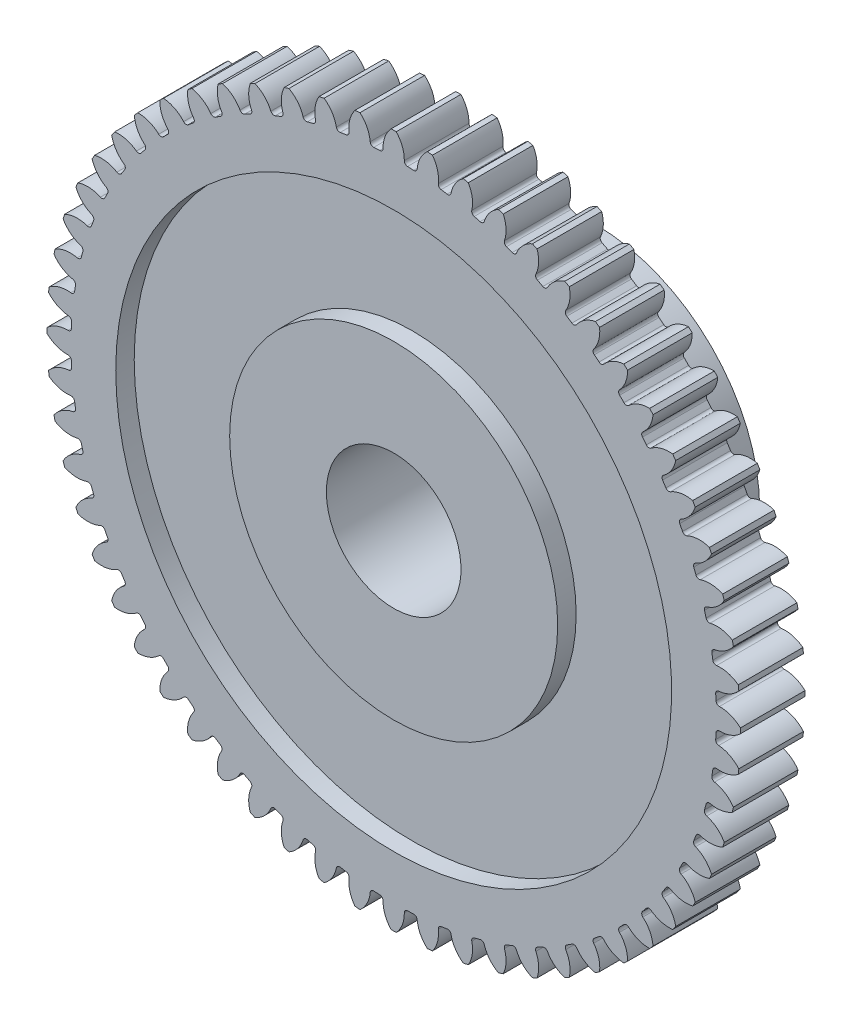
SolidWorks part; units mm, degrees
ref_plane "Front Plane" through (0, 0, 0) normal (0, 0, 1) x (1, 0, 0)
ref_plane "Top Plane" through (0, 0, 0) normal (0, 1, 0) x (1, 0, 0)
ref_plane "Right Plane" through (0, 0, 0) normal (1, 0, 0) x (0, 0, -1)
sketch "Sketch1" plane through (0, 0, 0) normal (1, 0, 0) x (0, 0, -1)
  line L0 (-4.7625, 0) -> (-4.7625, 16.3512)
  line L1 (-4.7625, 16.3512) -> (-1.7145, 16.3512)
  line L2 (-1.7145, 16.3512) -> (-1.7145, 7.7343)
  line L3 (-1.7145, 7.7343) -> (4.7625, 7.7343)
  line L4 (4.7625, 7.7343) -> (4.7625, 0)
  line L5 (4.7625, 0) -> (-4.7625, 0) construction
  line L6 (-4.7625, 3.175) -> (4.7625, 3.175)
  point P9 (-4.7625, 13.1064)
  dimension "OD" = 32.7025
  dimension "Face Width" = 3.048
  dimension "Hub Width" = 6.477
  dimension "Hub Diameter" = 15.4686
  dimension "For Shaft Diameter" = 6.35
  dimension "Overall Width" = 9.525
  dimension "Under Cut Diameter" = 26.2128
sketch "Sketch2" plane through (0, 0, 0) normal (0, 0, 1) x (1, 0, 0)
  line L0 (-0.6596, 15.1992) -> (-0.2403, 16.3512)
  line L1 (-0.2403, 16.3512) -> (0.2403, 16.3512)
  line L2 (0.2403, 16.3512) -> (0.6596, 15.1992)
  line L3 (0, 16.3512) -> (0, 0) construction
  line L4 (0, 0) -> (-0.8558, 16.3288) construction
  line L5 (0, 0) -> (0.8558, 16.3288) construction
  line L6 (-2.2447, 15.047) -> (-1.9481, 16.2366)
  line L7 (-1.9481, 16.2366) -> (-1.4702, 16.2868)
  line L8 (-1.4702, 16.2868) -> (-0.9328, 15.1849)
  line L9 (-1.7092, 16.2617) -> (0, 0) construction
  line L11 (-0.2403, 16.3512) -> (0, 16.3512) construction
  line L12 (-0.4156, 15.8696) -> (0.4156, 15.8696) construction
  circle A0 centre (0, 0) radius 15.875 construction
  circle A2 centre (0, 0) radius 16.3512
  circle A3 centre (0, 0) radius 15.2135
  arc A5 (-0.1201, 16.3512) -> (-0.4894, 15.2057) centre (0.9133, 15.3859) ccw
  arc A6 (0.4894, 15.2057) -> (0.1201, 16.3512) centre (-0.9133, 15.3859) ccw
  arc A7 (-1.1027, 15.1735) -> (-1.5897, 16.2742) centre (-2.5166, 15.2061) ccw
  arc A8 (-0.4156, 15.8696) -> (0.4156, 15.8696) centre (0, 0) cw
  point P3 (0, 15.875)
  point P5 (1.6594, 15.788)
  point P6 (13.7482, -7.9375)
  point P9 (3.3006, 15.5281)
  point P10 (4.9056, 15.098)
  point P11 (6.4569, 14.5025)
  point P12 (7.9375, 13.7482)
  point P13 (9.3311, 12.8431)
  point P14 (10.6224, 11.7974)
  point P15 (11.7974, 10.6224)
  point P16 (12.8431, 9.3311)
  point P17 (13.7482, 7.9375)
  point P18 (14.5025, 6.4569)
  point P19 (15.098, 4.9056)
  point P20 (15.5281, 3.3006)
  point P21 (15.788, 1.6594)
  point P22 (15.875, 0)
  point P23 (15.788, -1.6594)
  point P24 (15.5281, -3.3006)
  point P25 (15.098, -4.9056)
  point P26 (14.5025, -6.4569)
  point P27 (12.8431, -9.3311)
  point P28 (11.7974, -10.6224)
  point P29 (10.6224, -11.7974)
  point P30 (9.3311, -12.8431)
  point P31 (0, 0)
  point P55 (7.9375, -13.7482)
  point P56 (6.4569, -14.5025)
  point P57 (4.9056, -15.098)
  point P58 (3.3006, -15.5281)
  point P59 (1.6594, -15.788)
  point P61 (0, -15.875)
  point P62 (-1.6594, -15.788)
  point P63 (-3.3006, -15.5281)
  point P64 (-4.9056, -15.098)
  point P65 (-6.4569, -14.5025)
  point P66 (-7.9375, -13.7482)
  point P67 (-9.3311, -12.8431)
  point P68 (-10.6224, -11.7974)
  point P69 (-11.7974, -10.6224)
  point P70 (-12.8431, -9.3311)
  point P71 (-13.7482, -7.9375)
  point P72 (-14.5025, -6.4569)
  point P73 (-15.098, -4.9056)
  point P74 (-15.5281, -3.3006)
  point P75 (-15.788, -1.6594)
  point P76 (-15.875, 0)
  point P77 (-15.788, 1.6594)
  point P78 (-15.5281, 3.3006)
  point P79 (-15.098, 4.9056)
  point P80 (-14.5025, 6.4569)
  point P81 (-13.7482, 7.9375)
  point P82 (-12.8431, 9.3311)
  point P83 (-11.7974, 10.6224)
  point P84 (-10.6224, 11.7974)
  point P85 (-9.3311, 12.8431)
  point P86 (-7.9375, 13.7482)
  point P87 (-6.4569, 14.5025)
  point P88 (-4.9056, 15.098)
  point P89 (-3.3006, 15.5281)
  point P90 (-1.6594, 15.788)
  dimension "Gear Pitch Diameter" = 31.75
  dimension "Pressure Angle" = 20
  dimension "Addendum" = 0.4762
  dimension "Dedendum" = 0.6615
  dimension "D1" = 6
  dimension "D2" = 0.8312
  dimension "Number of Teeth" = 60
sketch "Sketch3" plane through (0, 0, 0) normal (1, 0, 0) x (0, 0, -1)
  line L0 (-4.7625, 16.3512) -> (-1.7145, 16.3512) construction
  line L1 (4.7625, 7.7343) -> (4.7625, 0) construction
  line L2 (-1.7145, 7.7343) -> (4.7625, 7.7343) construction
  line L3 (-1.7145, 16.3512) -> (-1.7145, 7.7343) construction
  line L4 (-4.7625, 0) -> (-4.7625, 16.3512) construction
  line L5 (-4.7625, 3.175) -> (4.7625, 3.175) construction
  line L6 (-4.7625, 16.3512) -> (-1.7145, 16.3512)
  line L7 (4.7625, 7.7343) -> (4.7625, 3.175)
  line L8 (-4.7625, 7.7343) -> (-3.8916, 7.7343)
  line L9 (-1.7145, 16.3512) -> (-1.7145, 13.1064)
  line L10 (-4.7625, 3.175) -> (-4.7625, 7.7343)
  line L11 (-4.7625, 3.175) -> (4.7625, 3.175)
  line L12 (-4.7625, 13.1064) -> (-3.8916, 13.1064)
  line L13 (-3.8916, 13.1064) -> (-3.8916, 7.7343)
  line L14 (-1.7145, 13.1064) -> (-2.5854, 13.1064)
  line L15 (-2.5854, 13.1064) -> (-2.5854, 7.7343)
  line L16 (-2.5854, 7.7343) -> (4.7625, 7.7343)
  line L17 (-4.7625, 13.1064) -> (-4.7625, 16.3512)
  dimension "D1" = 0.8709
revolve "Revolve1" add sketch "Sketch3" angle 360 about L5
sketch "Sketch4" plane through (0, 0, 4.7625) normal (0, 0, 1) x (1, 0, 0)
  arc A1 (-0.1201, 16.3512) -> (-0.4894, 15.2057) centre (0.9133, 15.3859) ccw construction
  arc A2 (-1.1027, 15.1735) -> (-1.5897, 16.2742) centre (-2.5166, 15.2061) ccw construction
  arc A3 (-0.1206, 16.3508) -> (-0.5007, 15.3609) centre (0.9133, 15.3859) ccw
  arc A4 (-1.1077, 15.3291) -> (-1.5892, 16.2738) centre (-2.5166, 15.2061) ccw
  circle A5 centre (0, 0) radius 16.3512 construction
  arc A6 (-0.1206, 16.3508) -> (-1.5892, 16.2738) centre (0, 0) ccw
  circle A7 centre (0, 0) radius 15.2135 construction
  arc A8 (-0.6526, 15.1995) -> (-0.9398, 15.1845) centre (0, 0) ccw
  arc A9 (-1.1077, 15.3291) -> (-0.9398, 15.1845) centre (-0.9496, 15.3429) ccw
  arc A10 (-0.6526, 15.1995) -> (-0.5007, 15.3609) centre (-0.6594, 15.3581) ccw
  dimension "D1" = 0.1587
extrude "Cut-Extrude1" cut sketch "Sketch4" against normal through all both and the other way through all
pattern_circular "CirPattern1" count 60 over 360 about axis through (0, 0, 0) along (0, 0, 1) of "Cut-Extrude1"
equation "\"Dedendum@Sketch2\" = 1.25 /  ( \"Number of Teeth@Sketch2\" / \"Gear Pitch Diameter@Sketch2\" ) "
equation "\"D1@Sketch2\"=360/\"Number of Teeth@Sketch2\""
equation "\"D1@Sketch4\"=.3/(\"Number of Teeth@Sketch2\"/\"Gear Pitch Diameter@Sketch2\")"
equation "\"D1@CirPattern1\"=\"Number of Teeth@Sketch2\""
equation "\"D2@Sketch2\"=1.5708/(\"Number of Teeth@Sketch2\"/\"Gear Pitch Diameter@Sketch2\")"
equation "\"D1@Sketch3\"=\"Face Width@Sketch1\"/3.5"
